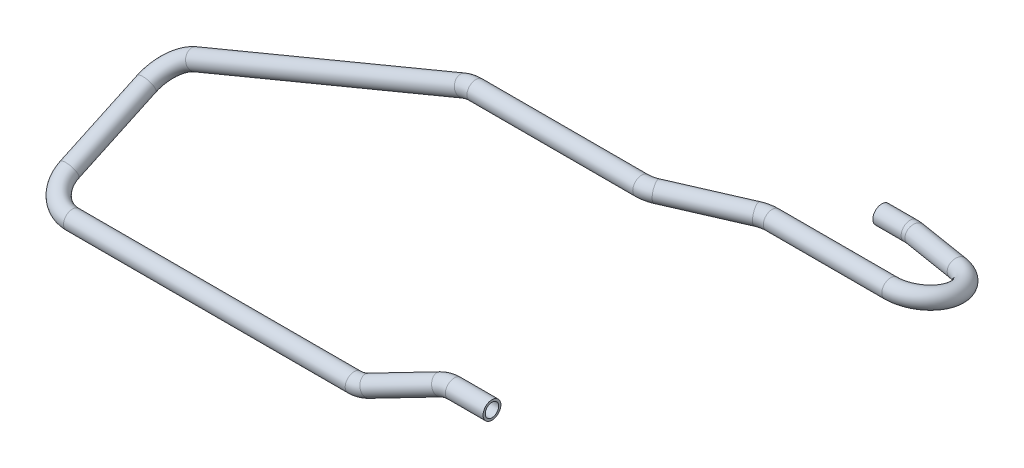
SolidWorks part; units mm, degrees
ref_plane "Plane1" through (0, 0, 0) normal (0, 0, 1) x (1, 0, 0)
ref_plane "Plane2" through (0, 0, 0) normal (0, 1, 0) x (1, 0, 0)
ref_plane "Plane3" through (0, 0, 0) normal (1, 0, 0) x (0, 0, -1)
sketch3d "3DSketch1"
  line L0 (0, 0, 0) -> (-25.3274, 0, 0)
  line L1 (-30, -22, 8) -> (-30, -22, 0) construction
  line L2 (-30, -22, 8) -> (-80, -22, 8) construction
  line L3 (-34.2318, -1.862, 0.6771) -> (-75.7682, -20.138, 7.3229)
  line L4 (-295, 11.0321, -62.8376) -> (-295, -13.125, -11.0325)
  line L5 (-84.6726, -22, 8) -> (-274, -22, 8)
  line L6 (0, 0, 0) -> (0, 0, -151) construction
  line L7 (0, 0, -151) -> (0, 93.9998, -151) construction
  line L8 (-278.5293, 25.4054, -79) -> (-97.8655, 100.3953, -79)
  line L9 (-30, -22, 0) -> (-30, 0, 0) construction
  line L11 (-89.8148, 101.9998, -79) -> (21.6177, 101.9998, -79)
  line L12 (26, 101.9998, -79) -> (26, 101.9998, -103) construction
  line L13 (26, 101.9998, -103) -> (81, 101.9998, -103) construction
  line L14 (30.0165, 101.9998, -80.7527) -> (76.9835, 101.9998, -101.2473)
  line L15 (85.3823, 101.9998, -103) -> (165, 101.9998, -103)
  line L16 (186, 101.9998, -103) -> (186, 101.9998, -151) construction
  line L17 (186, 101.9998, -151) -> (186, 93.9998, -151) construction
  line L18 (186, 93.9998, -151) -> (186, 101.9998, -103) construction
  line L19 (130.0181, 93.9998, -151) -> (111, 93.9998, -151)
  line L20 (111, 93.9998, -151) -> (0, 93.9998, -151) construction
  line L21 (133.9469, 94.0607, -150.6343) -> (168.9287, 95.156, -144.0628)
  line L22 (168.9287, 95.156, -144.0628) -> (186, 95.6905, -140.8559) construction
  line L25 (-295, 18.5688, -79) -> (-295, 18.5688, 8) construction
  line L26 (-295, 18.5688, 8) -> (-295, -22, 8) construction
  line L27 (-94, 101.9998, -79) -> (-295, 101.9998, -79) construction
  line L28 (-295, 101.9998, -79) -> (-295, 15.9569, -79) construction
  arc A0 (-25.3274, 0, 0) -> (-34.2318, -1.862, 0.6771) centre (-25.3274, -19.7357, 7.1766) ccw
  arc A1 (-274, -22, 8) -> (-295, -13.125, -11.0325) centre (-274, -13.125, -11.0325) ccw
  arc A2 (-295, 11.0321, -62.8376) -> (-278.5293, 25.4054, -79) centre (-275.3448, 17.7334, -59.7127) ccw
  arc A3 (133.9469, 94.0607, -150.6343) -> (130.0181, 93.9998, -151) centre (130.0181, 97.4522, -130.2857) ccw
  arc A4 (-97.8655, 100.3953, -79) -> (-89.8148, 101.9998, -79) centre (-89.8148, 80.9998, -79) ccw
  arc A5 (85.3823, 101.9998, -103) -> (76.9835, 101.9998, -101.2473) centre (85.3823, 101.9998, -82) ccw
  arc A6 (165, 101.9998, -103) -> (168.9287, 95.156, -144.0628) centre (165, 98.5474, -123.7143) ccw
  arc A7 (-75.7682, -20.138, 7.3229) -> (-84.6726, -22, 8) centre (-84.6726, -2.2643, 0.8234) ccw
  arc A8 (21.6177, 101.9998, -79) -> (30.0165, 101.9998, -80.7527) centre (21.6177, 101.9998, -100) ccw
  point P13 (-80, -22, 8)
  point P14 (-295, -22, 8)
  point P19 (-295, 18.5688, -79)
  point P21 (-295, 18.5688, -79)
  point P22 (-267.9507, -0.0802, -68.0194)
  point P23 (-274, -32.1575, -19.9074)
  point P26 (-295, 18.5688, -79)
  point P33 (-94, 101.9998, -79)
  point P34 (-89.8148, 80.9998, -100)
  point P43 (81, 101.9998, -103)
  point P45 (85.3823, 122.9998, -82)
  point P47 (165, 119.2617, -127.1667)
  point P50 (132, 93.9998, -151)
  point P51 (130.0181, 118.1664, -133.7381)
  point P54 (-30, 0, 0)
  point P58 (26, 101.9998, -79)
  point P60 (21.6177, 122.9998, -100)
  point P62 (-25.3274, -12.5591, 26.9123)
  point P66 (-80, -22, 8)
  point P68 (-84.6726, -9.4409, -18.9123)
  point P69 (387.5186, 101.9998, -103)
  dimension "D4" = 22
  dimension "D5" = 21
  dimension "D9" = 151
  dimension "D10" = 111
  dimension "D14" = 21
  dimension "D21" = 21
  dimension "D22" = 21
  dimension "D23" = 21
  dimension "D24" = 21
  dimension "D7" = 21
  dimension "D11" = 21
  dimension "D8" = 21
  dimension "D25" = 8
  dimension "D2" = 50
  dimension "D3" = 30
  dimension "D6" = 87
  dimension "D13" = 120
  dimension "D12" = 215
  dimension "D15" = 24
  dimension "D17" = 105
  dimension "D16" = 55
  dimension "D18" = 93.9998
  dimension "D19" = 8
  dimension "D20" = 75
  dimension "D26" = 25
ref_plane "Plane4" through (0, 0, 0) normal (-1, 0, 0) x (0, 0, 1)
sketch "Sketch1" plane through (0, 0, 0) normal (-1, 0, 0) x (0, 0, 1)
  circle A0 centre (0, 0) radius 6
  circle A1 centre (0, 0) radius 4.5
  dimension "D1" = 9
  dimension "D2" = 12
sweep "Sweep1" add profiles "Sketch1" path "3DSketch1"
